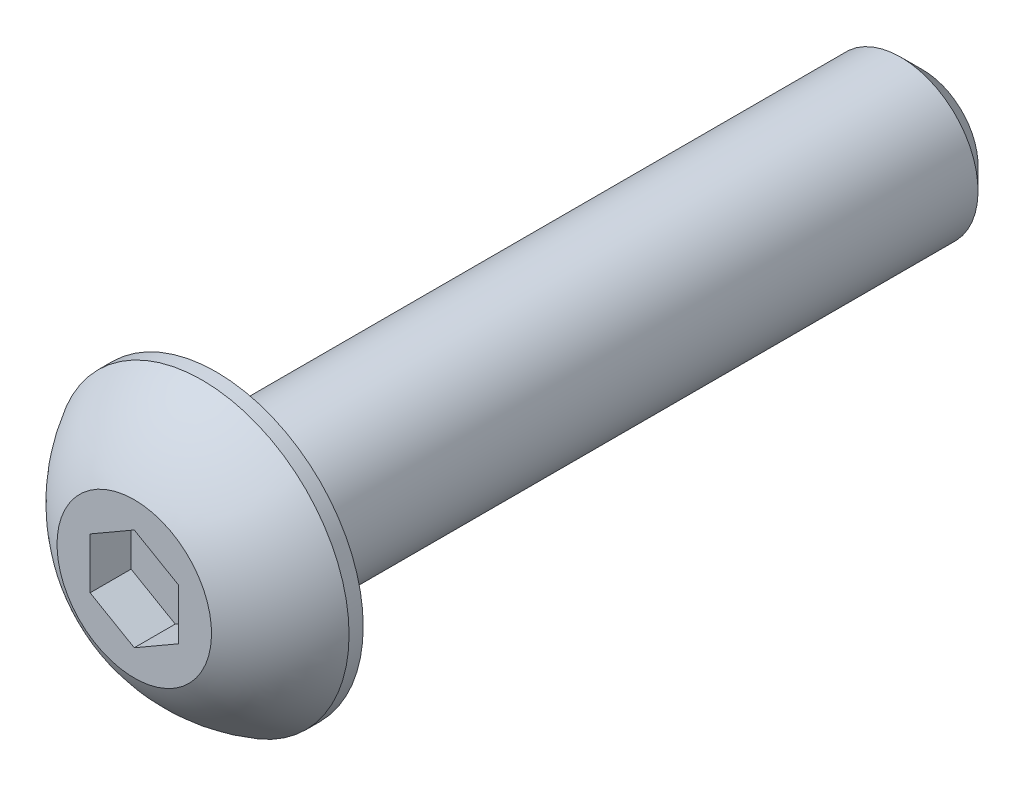
SolidWorks part; units mm, degrees
material "18-8 SSTL"
ref_plane "Front" through (0, 0, 0) normal (0, 0, 1) x (1, 0, 0)
ref_plane "Top" through (0, 0, 0) normal (0, 1, 0) x (1, 0, 0)
ref_plane "Right" through (0, 0, 0) normal (1, 0, 0) x (0, 0, -1)
sketch "Sketch1" plane through (0, 0, 0) normal (1, 0, 0) x (0, 0, -1)
  line L0 (0, 0) -> (-2.2098, 0) construction
  line L1 (0, 0) -> (19.05, 0)
  line L2 (0, 0) -> (0, 2.0828)
  line L3 (0, 2.0828) -> (19.05, 2.0828)
  line L4 (19.05, 0) -> (19.05, 2.0828)
  line L5 (0, -2.0828) -> (19.05, -2.0828) construction
  dimension "D1" = 19.05
  dimension "Thread Dia" = 4.1656
  dimension "Length" = 19.05
  dimension "Head Height" = 2.2098
revolve "Revolve1" add sketch "Sketch1" angle 360 about L0
ref_plane "Plane1" through (0, 0, 2.2098) normal (0, 0, 1) x (1, 0, 0)
chamfer "Chamfer1" distance 0.5953 angle 45 1 edges at (0, 2.0828, -19.05)
sketch "Sketch4" plane through (0, 0, 0) normal (0, 0, 1) x (1, 0, 0)
  circle A0 centre (0, 0) radius 3.9624
  dimension "Head Dia" = 7.9248
extrude "Extrude1" add sketch "Sketch4" along normal up to surface (2.2098 mm away) up to plane "Plane1"
sketch "Sketch9" plane through (0, 0, 0) normal (1, 0, 0) x (0, 0, -1)
  line L0 (0, 3.9624) -> (-0.381, 3.9624)
  line L1 (0, 3.9624) -> (0, 4.3434)
  line L2 (0, 4.3434) -> (-2.5908, 4.3434)
  line L3 (0, 0) -> (-2.2098, 0) construction
  line L4 (-2.5908, 4.3434) -> (-2.5908, 2.0828)
  line L5 (-2.5908, 2.0828) -> (-2.2098, 2.0828)
  line L6 (0, 0) -> (0, 2.0828) construction
  line L10 (0, 3.9624) -> (-2.2098, 3.9624) construction
  line L11 (0, 2.0828) -> (19.05, 2.0828) construction
  line L12 (-2.2098, 3.9624) -> (-2.2098, -3.9624) construction
  arc A0 (-2.2098, 2.0828) -> (-0.381, 3.9624) centre (1.8112, 0) cw
  dimension "Side Head Height" = 0.381
revolve "Cut-Revolve3" cut sketch "Sketch9" angle 360 about L3
sketch "Sketch6" plane through (0, 0, 2.2098) normal (0, 0, 1) x (1, 0, 0)
  line L1 (0, -1.3748) -> (1.1906, -0.6874)
  line L2 (1.1906, -0.6874) -> (1.1906, 0.6874)
  line L3 (1.1906, 0.6874) -> (0, 1.3748)
  line L4 (0, 1.3748) -> (-1.1906, 0.6874)
  line L5 (-1.1906, 0.6874) -> (-1.1906, -0.6874)
  line L6 (-1.1906, -0.6874) -> (0, -1.3748)
  circle A0 centre (0, 0) radius 1.1906 construction
  dimension "Hex" = 2.3813
extrude "Cut-Extrude1" cut sketch "Sketch6" against normal blind 1.1049
equation "\"D1@Cut-Extrude1\"=\"Head Height@Sketch1\"/2"
